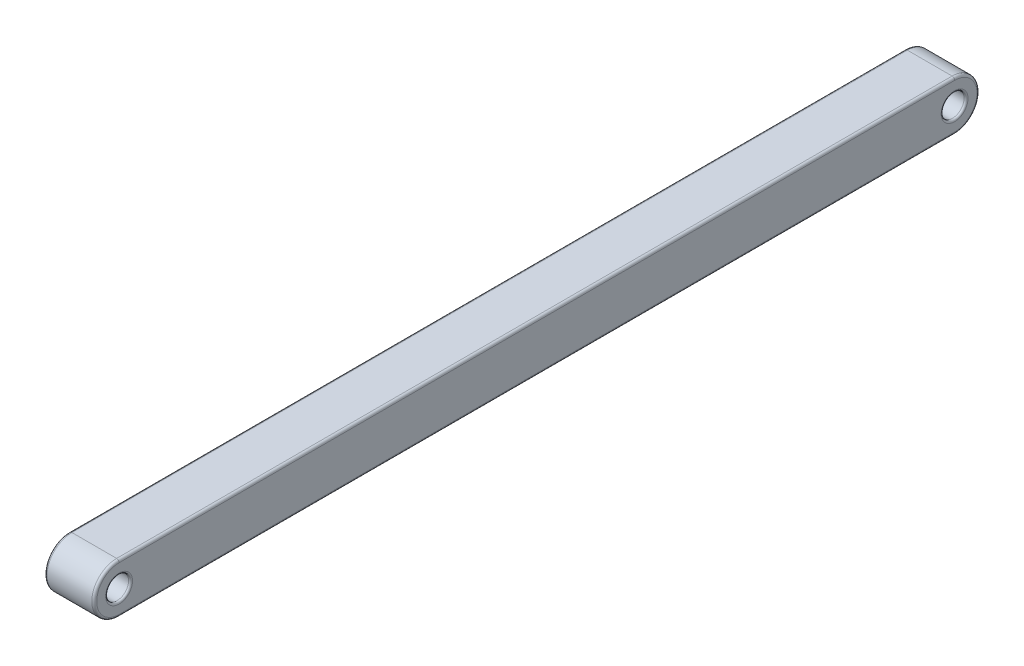
SolidWorks part; units mm, degrees
ref_plane "Front Plane" through (0, 0, 0) normal (0, 0, 1) x (1, 0, 0)
ref_plane "Top Plane" through (0, 0, 0) normal (0, 1, 0) x (1, 0, 0)
ref_plane "Right Plane" through (0, 0, 0) normal (1, 0, 0) x (0, 0, -1)
sketch "Sketch1" plane through (0, 0, 0) normal (1, 0, 0) x (0, 0, -1)
  line L1 (0, 0) -> (40, 0)
  line L2 (0, 0) -> (0, -2.5) construction
  line L3 (0, -2.5) -> (40, -2.5)
  line L4 (40, 0) -> (40, -2.5) construction
  line L5 (0, 0) -> (-1, 0)
  line L6 (0, 0) -> (0, -2.5) construction
  line L7 (0, -2.5) -> (-1, -2.5)
  line L8 (-1, 0) -> (-1, -2.5) construction
  line L9 (40, 0) -> (41, 0)
  line L10 (40, 0) -> (40, -2.5) construction
  line L11 (40, -2.5) -> (41, -2.5)
  line L12 (41, 0) -> (41, -2.5) construction
  line L16 (0, -1.25) -> (-1, -1.25) construction
  line L17 (40, -1.25) -> (41, -1.25) construction
  circle A0 centre (-1, -1.25) radius 0.575
  arc A1 (-1, -2.5) -> (-1, 0) centre (-1, -1.25) cw
  circle A2 centre (41, -1.25) radius 0.575
  arc A3 (41, 0) -> (41, -2.5) centre (41, -1.25) cw
  dimension "D1" = 1.15
  dimension "D4" = 1.15
  dimension "D2" = 2.5
  dimension "D3" = 2.5
  dimension "D5" = 42
  dimension "D6" = 2.5
  dimension "D7" = 1
  dimension "D8" = 1
extrude "Boss-Extrude1" add sketch "Sketch1" along normal blind 2.5 contours A3 L9 L1 L5 A1 L7 L3 L11 A2 A0
fillet "Fillet1" radius 0.125 8 edges at (2.5, -1.25, -42.25) (2.5, 0, -20) (2.5, -1.25, 2.25) (0, -1.25, -42.25) (0, 0, -20) (0, -1.25, 2.25) (2.5, -2.5, -20) (0, -2.5, -20)
fillet "Fillet2" radius 0.1 4 edges at (0, -1.25, -41.575) (2.5, -1.25, -41.575) (0, -1.25, 0.425) (2.5, -1.25, 0.425)
